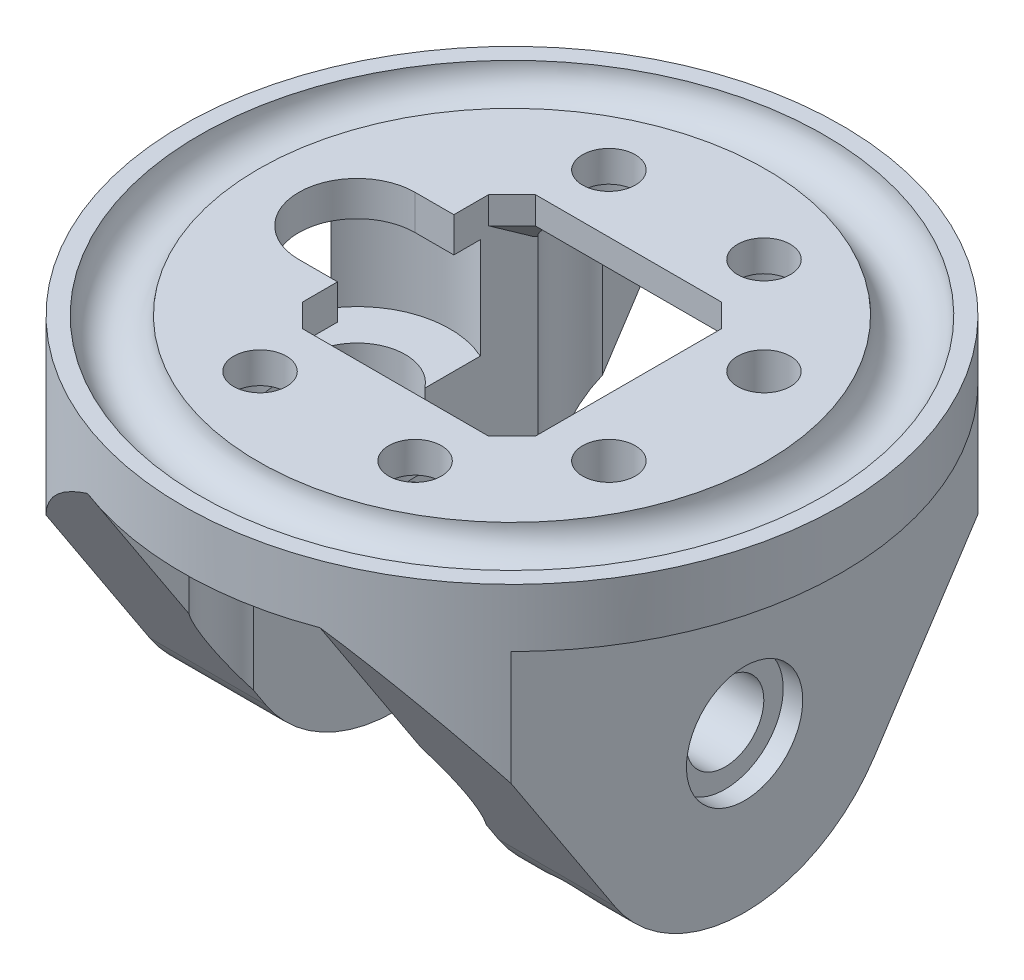
SolidWorks part; units mm, degrees
material "Markforged"
ref_plane "Front Plane" through (0, 0, 0) normal (0, 0, 1) x (1, 0, 0)
ref_plane "Top Plane" through (0, 0, 0) normal (0, 1, 0) x (1, 0, 0)
ref_plane "Right Plane" through (0, 0, 0) normal (1, 0, 0) x (0, 0, -1)
sketch "Sketch2" plane through (0, 0, 0) normal (0, 0, 1) x (1, 0, 0)
  line L0 (0, 0) -> (0, 2.3813)
  line L1 (0, 2.3813) -> (-20.7678, 2.3812)
  line L2 (-25.5872, 2.3812) -> (-26.9875, 2.3812)
  line L3 (-26.9875, 2.3812) -> (-26.9875, -2.3813)
  line L4 (-26.9875, -2.3813) -> (0, -2.3813)
  line L5 (0, -2.3813) -> (0, 0)
  line L6 (-22.2794, 2.5082) -> (-22.0319, 2.5082) construction
  arc A0 (-25.5872, 2.3812) -> (-20.7678, 2.3812) centre (-23.1775, 2.5082) ccw
  dimension "D5" = 2.413
  dimension "D1" = 0.254
  dimension "D2" = 26.9875
  dimension "D3" = 23.1775
  dimension "D4" = 4.7625
revolve "Revolve1" add sketch "Sketch2" angle 360 about L0
sketch "Sketch3" plane through (0, 2.3813, 0) normal (0, 1, 0) x (1, 0, 0)
  line L0 (-12.7, 0) -> (0, 0) construction
  line L1 (-9.525, -9.525) -> (9.525, -9.525)
  line L2 (-9.525, -9.525) -> (-9.525, -4.7625)
  line L3 (-9.525, 9.525) -> (9.525, 9.525)
  line L4 (9.525, -9.525) -> (9.525, 9.525)
  line L5 (-9.525, -9.525) -> (9.525, 9.525) construction
  line L6 (-9.525, 9.525) -> (9.525, -9.525) construction
  line L7 (-12.7, -4.7625) -> (-9.525, -4.7625)
  line L8 (-12.7, 4.7625) -> (-9.525, 4.7625)
  line L9 (-9.525, -4.7625) -> (-9.525, 0) construction
  line L10 (-9.525, 4.7625) -> (-9.525, 9.525)
  line L11 (-9.525, 0) -> (-9.525, 4.7625) construction
  arc A0 (-12.7, 4.7625) -> (-12.7, -4.7625) centre (-12.7, 0) ccw
  arc A1 (-12.7, -4.7625) -> (-7.9375, 0) centre (-12.7, 0) ccw construction
  arc A2 (-7.9375, 0) -> (-12.7, 4.7625) centre (-12.7, 0) ccw construction
  point P0 (0, 0)
  dimension "D4" = 9.525
  dimension "D1" = 19.05
  dimension "D2" = 12.7
  dimension "D3" = 19.05
extrude "Cut-Extrude1" cut sketch "Sketch3" against normal through all
sketch "Sketch4" plane through (0, -2.3813, 0) normal (0, -1, 0) x (1, 0, 0)
  circle A0 centre (-12.7, 0) radius 7.62
  dimension "D1" = 15.24
extrude "Cut-Extrude2" cut sketch "Sketch4" against normal blind 1.905
sketch "Sketch5" plane through (0, -2.3813, 0) normal (0, -1, 0) x (1, 0, 0)
  line L0 (-9.525, -25.2507) -> (-9.525, 25.2507)
  line L1 (-19.05, 19.116) -> (-19.05, -19.116)
  line L2 (-19.05, 0) -> (-12.7, 0) construction
  line L3 (-12.7, 0) -> (-9.525, 0) construction
  line L4 (-9.525, 9.525) -> (-9.525, 6.927) construction
  line L5 (0, -26.9875) -> (0, 0) construction
  line L6 (9.525, -25.2507) -> (9.525, 25.2507)
  line L7 (19.05, 19.116) -> (19.05, -19.116)
  circle A0 centre (0, 0) radius 26.9875 construction
  arc A1 (-19.05, -19.116) -> (-9.525, -25.2507) centre (0, 0) ccw
  arc A2 (-9.525, 25.2507) -> (-19.05, 19.116) centre (0, 0) ccw
  arc A3 (9.525, 25.2507) -> (19.05, 19.116) centre (0, 0) cw
  arc A4 (19.05, -19.116) -> (9.525, -25.2507) centre (0, 0) cw
  dimension "D1" = 6.35
extrude "Boss-Extrude1" add sketch "Sketch5" along normal blind 50.8
sketch "Sketch6" plane through (0, 0, 0) normal (1, 0, 0) x (0, 0, -1)
  line L0 (-25.2507, -2.3813) -> (-25.2507, -53.1812)
  line L1 (-25.2507, -53.1812) -> (25.2507, -53.1812)
  line L2 (25.2507, -53.1812) -> (25.2507, -2.3813)
  line L3 (0, -2.3813) -> (0, -17.7482) construction
  line L4 (-19.116, -2.3813) -> (19.116, -2.3813) construction
  line L5 (-10.6231, -24.7081) -> (-25.2507, -2.3813)
  line L6 (10.6231, -24.7081) -> (25.2507, -2.3813)
  circle A0 centre (0, -17.7482) radius 19.05 construction
  arc A1 (-10.6231, -24.7081) -> (10.6231, -24.7081) centre (0, -17.7482) ccw
  circle A2 centre (0, -17.7482) radius 3.175
  dimension "D2" = 38.1
  dimension "D3" = 12.7
  dimension "D4" = 6.35
  dimension "D1" = 15.367
extrude "Cut-Extrude3" cut sketch "Sketch6" against normal through all both and the other way through all
sketch "Sketch7" plane through (0, -2.3813, 0) normal (0, 1, 0) x (1, 0, 0)
  circle A0 centre (-12.7, 0) radius 7.62
  arc A1 (-9.525, 6.927) -> (-19.05, 4.2121) centre (-12.7, 0) ccw construction
extrude "Cut-Extrude4" cut sketch "Sketch7" against normal blind 6.35
sketch "Sketch8" plane through (0, -8.7313, 0) normal (0, 1, 0) x (1, 0, 0)
  circle A0 centre (-12.7, 0) radius 3.9688
  dimension "D1" = 7.9375
extrude "Cut-Extrude5" cut sketch "Sketch8" against normal blind 2.7686
sketch "Sketch9" plane through (0, -11.4999, 0) normal (0, 1, 0) x (1, 0, 0)
  circle A0 centre (-12.7, 0) radius 3.2385
  dimension "D1" = 6.477
extrude "Cut-Extrude6" cut sketch "Sketch9" against normal blind 0.635
chamfer "Chamfer1" distance 1.905 angle 45 4 edges at (-9.525, 0, 9.525) (9.525, 0, 9.525) (9.525, 0, -9.525) (-9.525, 0, -9.525)
chamfer "Chamfer2" distance 2.54 angle 45 6 edges at (0, -2.3813, 9.525) (0, -2.3813, -9.525) (-8.5725, -2.3813, 8.5725) (8.5725, -2.3813, 8.5725) (8.5725, -2.3813, -8.5725) (-8.5725, -2.3813, -8.5725)
sketch "Sketch10" plane through (0, 0, 0) normal (0, 1, 0) x (1, 0, 0)
  line L0 (9.525, 6.35) -> (9.525, 0) construction
  line L1 (-6.35, 14.2875) -> (6.35, 14.2875) construction
  line L2 (-6.35, 14.2875) -> (-6.35, -14.2875) construction
  line L3 (-6.35, -14.2875) -> (6.35, -14.2875) construction
  line L4 (6.35, 14.2875) -> (6.35, -14.2875) construction
  line L5 (-6.35, 14.2875) -> (6.35, -14.2875) construction
  line L6 (-6.35, -14.2875) -> (6.35, 14.2875) construction
  line L7 (9.525, 6.35) -> (14.2875, 6.35) construction
  line L8 (14.2875, 6.35) -> (19.05, 6.35) construction
  line L9 (9.525, 3.175) -> (9.525, -3.175) construction
  line L10 (19.05, -3.175) -> (19.05, 3.175) construction
  line L11 (9.525, -7.62) -> (9.525, 7.62) construction
  line L12 (9.525, 0) -> (9.525, -6.35) construction
  line L13 (9.525, -6.35) -> (14.2875, -6.35) construction
  line L14 (14.2875, -6.35) -> (19.05, -6.35) construction
  circle A0 centre (-6.35, 14.2875) radius 2.159
  circle A1 centre (-6.35, 14.2875) radius 3.175 construction
  circle A2 centre (-6.35, -14.2875) radius 2.159
  circle A3 centre (6.35, -14.2875) radius 2.159
  circle A4 centre (6.35, 14.2875) radius 2.159
  circle A5 centre (14.2875, 6.35) radius 2.159
  circle A6 centre (14.2875, -6.35) radius 2.159
  point P0 (0, 0)
  dimension "D1" = 4.318
  dimension "D2" = 6.35
  dimension "D3" = 12.7
  dimension "D4" = 28.575
  dimension "D5" = 12.7
extrude "Cut-Extrude7" cut sketch "Sketch10" against normal through all both and the other way through all
sketch "Sketch11" plane through (0, 2.3813, 0) normal (0, 1, 0) x (1, 0, 0)
  circle A0 centre (-6.35, 14.2875) radius 4.1275
  circle A1 centre (6.35, 14.2875) radius 4.1275
  circle A2 centre (6.35, -14.2875) radius 4.1275
  circle A3 centre (-6.35, -14.2875) radius 4.1275
  dimension "D1" = 8.255
extrude "Cut-Extrude8" cut sketch "Sketch11" against normal through all from offset 2.54 offset against normal yes
sketch "Sketch12" plane through (0, 2.3813, 0) normal (0, 1, 0) x (1, 0, 0)
  circle A0 centre (14.2875, 6.35) radius 3.556
  circle A1 centre (14.2875, -6.35) radius 3.556
  dimension "D1" = 7.112
extrude "Cut-Extrude9" cut sketch "Sketch12" against normal through all from offset 22.225 offset against normal yes
sketch "Sketch13" plane through (19.05, 0, 0) normal (1, 0, 0) x (0, 0, -1)
  circle A0 centre (0, -17.7482) radius 4.7625
  dimension "D1" = 9.525
extrude "Cut-Extrude10" cut sketch "Sketch13" against normal blind 1.6002
